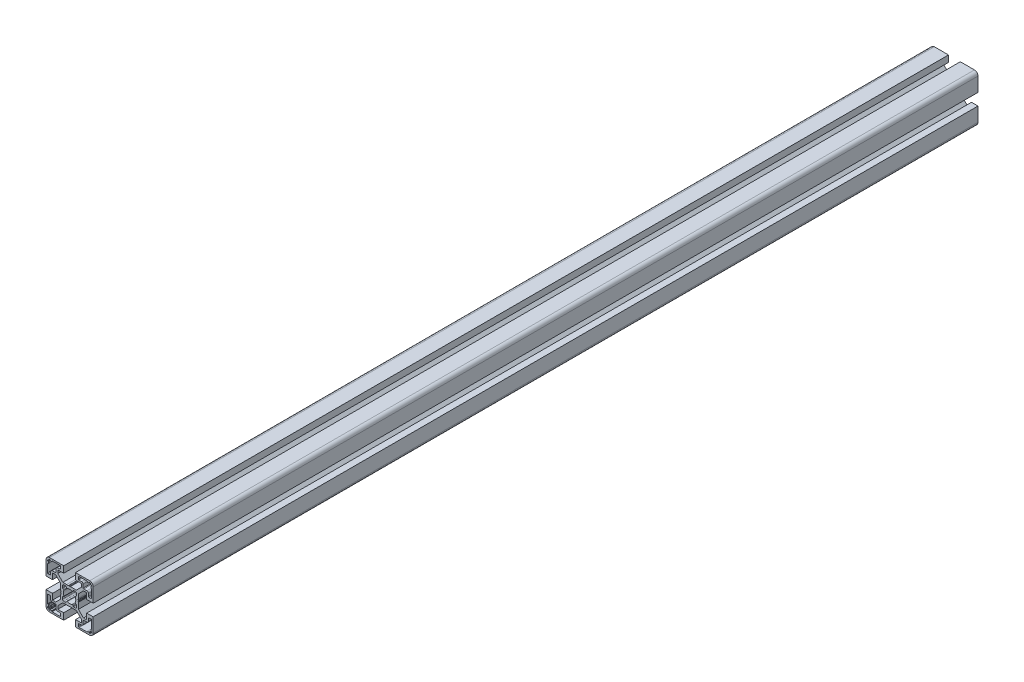
SolidWorks part; units mm, degrees
ref_plane "Front Plane" through (0, 0, 0) normal (0, 0, 1) x (1, 0, 0)
ref_plane "Top Plane" through (0, 0, 0) normal (0, 1, 0) x (1, 0, 0)
ref_plane "Right Plane" through (0, 0, 0) normal (1, 0, 0) x (0, 0, -1)
sketch "Sketch1" plane through (0, 0, 0) normal (0, 0, 1) x (1, 0, 0)
  line L0 (-11.7678, -10) -> (-14.5, -10)
  line L1 (-14.5, -10) -> (-14.5, -5)
  line L2 (-14.5, -5) -> (-20, -5)
  line L3 (-20, -5) -> (-20, -17)
  line L4 (-17, -20) -> (-5, -20)
  line L5 (-5, -20) -> (-5, -14.5)
  line L6 (-5, -14.5) -> (-10, -14.5)
  line L7 (-10, -14.5) -> (-10, -11.7678)
  line L8 (-10, -11.7678) -> (-5.7322, -7.5)
  line L9 (-5.7322, -7.5) -> (-0.6536, -7.5)
  line L10 (-0.4036, -7.433) -> (0, -7.2)
  line L11 (0, -7.2) -> (0.4036, -7.433)
  line L12 (0.9036, -7.433) -> (1.2189, -7.251)
  line L13 (1.2189, -7.251) -> (2.5, -7.5)
  line L14 (2.5, -7.5) -> (5.7322, -7.5)
  line L15 (5.7322, -7.5) -> (10, -11.7678)
  line L16 (10, -11.7678) -> (10, -14.5)
  line L17 (10, -14.5) -> (5, -14.5)
  line L18 (5, -14.5) -> (5, -20)
  line L19 (5, -20) -> (17, -20)
  line L20 (20, -17) -> (20, -5)
  line L21 (20, -5) -> (14.5, -5)
  line L22 (14.5, -5) -> (14.5, -10)
  line L23 (14.5, -10) -> (11.7678, -10)
  line L24 (11.7678, -10) -> (7.5, -5.7322)
  line L25 (7.5, -5.7322) -> (7.5, -0.6536)
  line L26 (7.433, -0.4036) -> (7.2, 0)
  line L27 (7.2, 0) -> (7.433, 0.4036)
  line L28 (7.433, 0.9036) -> (7.251, 1.2189)
  line L29 (7.251, 1.2189) -> (7.5, 2.5)
  line L30 (7.5, 2.5) -> (7.5, 5.7322)
  line L31 (7.5, 5.7322) -> (11.7678, 10)
  line L32 (11.7678, 10) -> (14.5, 10)
  line L33 (14.5, 10) -> (14.5, 5)
  line L34 (14.5, 5) -> (20, 5)
  line L35 (20, 5) -> (20, 17)
  line L36 (17, 20) -> (5, 20)
  line L37 (5, 20) -> (5, 14.5)
  line L38 (5, 14.5) -> (10, 14.5)
  line L39 (10, 14.5) -> (10, 11.7678)
  line L40 (10, 11.7678) -> (5.7322, 7.5)
  line L41 (5.7322, 7.5) -> (0.6536, 7.5)
  line L42 (0.4036, 7.433) -> (0, 7.2)
  line L43 (0, 7.2) -> (-0.4036, 7.433)
  line L44 (-0.9036, 7.433) -> (-1.2189, 7.251)
  line L45 (-1.2189, 7.251) -> (-2.5, 7.5)
  line L46 (-2.5, 7.5) -> (-5.7322, 7.5)
  line L47 (-5.7322, 7.5) -> (-10, 11.7678)
  line L48 (-10, 11.7678) -> (-10, 14.5)
  line L49 (-10, 14.5) -> (-5, 14.5)
  line L50 (-5, 14.5) -> (-5, 20)
  line L51 (-5, 20) -> (-17, 20)
  line L52 (-20, 17) -> (-20, 5)
  line L53 (-20, 5) -> (-14.5, 5)
  line L54 (-14.5, 5) -> (-14.5, 10)
  line L55 (-14.5, 10) -> (-11.7678, 10)
  line L56 (-11.7678, 10) -> (-7.5, 5.7322)
  line L57 (-7.5, 5.7322) -> (-7.5, 0.6536)
  line L58 (-7.433, 0.4036) -> (-7.2, 0)
  line L59 (-7.2, 0) -> (-7.433, -0.4036)
  line L60 (-7.433, -0.9036) -> (-7.251, -1.2189)
  line L61 (-7.251, -1.2189) -> (-7.5, -2.5)
  line L62 (-7.5, -2.5) -> (-7.5, -5.7322)
  line L63 (-7.5, -5.7322) -> (-11.7678, -10)
  line L64 (7.5, 16.5) -> (7.5, 18.2)
  line L65 (8, 18.7) -> (14.8, 18.7)
  line L66 (15, 18.5) -> (15, 18.2)
  line L67 (15.2, 18) -> (16.4, 18)
  line L68 (16.6, 18.2) -> (16.6, 18.5)
  line L69 (16.8, 18.7) -> (17.3, 18.7)
  line L70 (17.6, 18.4) -> (17.6, 17.9)
  line L71 (17.9, 17.6) -> (18.4, 17.6)
  line L72 (18.7, 17.3) -> (18.7, 16.8)
  line L73 (18.5, 16.6) -> (18.2, 16.6)
  line L74 (18, 16.4) -> (18, 15.2)
  line L75 (18.2, 15) -> (18.5, 15)
  line L76 (18.7, 14.8) -> (18.7, 8)
  line L77 (18.2, 7.5) -> (16.5, 7.5)
  line L78 (16, 8) -> (16, 10.2)
  line L79 (14.7, 11.5) -> (12, 11.5)
  line L80 (11.5, 12) -> (11.5, 14.7)
  line L81 (10.2, 16) -> (8, 16)
  line L82 (14.8, -18.7) -> (8, -18.7)
  line L83 (7.5, -18.2) -> (7.5, -16.5)
  line L84 (8, -16) -> (10.2, -16)
  line L85 (11.5, -14.7) -> (11.5, -12)
  line L86 (12, -11.5) -> (14.7, -11.5)
  line L87 (16, -10.2) -> (16, -8)
  line L88 (16.5, -7.5) -> (18.2, -7.5)
  line L89 (18.7, -8) -> (18.7, -14.8)
  line L90 (18.5, -15) -> (18.2, -15)
  line L91 (18, -15.2) -> (18, -16.4)
  line L92 (18.2, -16.6) -> (18.5, -16.6)
  line L93 (18.7, -16.8) -> (18.7, -17.3)
  line L94 (18.4, -17.6) -> (17.9, -17.6)
  line L95 (17.6, -17.9) -> (17.6, -18.4)
  line L96 (17.3, -18.7) -> (16.8, -18.7)
  line L97 (16.6, -18.5) -> (16.6, -18.2)
  line L98 (16.4, -18) -> (15.2, -18)
  line L99 (15, -18.2) -> (15, -18.5)
  line L100 (-18.7, 16.8) -> (-18.7, 17.3)
  line L101 (-18.4, 17.6) -> (-17.9, 17.6)
  line L102 (-17.6, 17.9) -> (-17.6, 18.4)
  line L103 (-17.3, 18.7) -> (-16.8, 18.7)
  line L104 (-16.6, 18.5) -> (-16.6, 18.2)
  line L105 (-16.4, 18) -> (-15.2, 18)
  line L106 (-15, 18.2) -> (-15, 18.5)
  line L107 (-14.8, 18.7) -> (-8, 18.7)
  line L108 (-7.5, 18.2) -> (-7.5, 16.5)
  line L109 (-8, 16) -> (-10.2, 16)
  line L110 (-11.5, 14.7) -> (-11.5, 12)
  line L111 (-12, 11.5) -> (-14.7, 11.5)
  line L112 (-16, 10.2) -> (-16, 8)
  line L113 (-16.5, 7.5) -> (-18.2, 7.5)
  line L114 (-18.7, 8) -> (-18.7, 14.8)
  line L115 (-18.5, 15) -> (-18.2, 15)
  line L116 (-18, 15.2) -> (-18, 16.4)
  line L117 (-18.2, 16.6) -> (-18.5, 16.6)
  line L118 (-18.7, -14.8) -> (-18.7, -8)
  line L119 (-18.2, -7.5) -> (-16.5, -7.5)
  line L120 (-16, -8) -> (-16, -10.2)
  line L121 (-14.7, -11.5) -> (-12, -11.5)
  line L122 (-11.5, -12) -> (-11.5, -14.7)
  line L123 (-10.2, -16) -> (-8, -16)
  line L124 (-7.5, -16.5) -> (-7.5, -18.2)
  line L125 (-8, -18.7) -> (-14.8, -18.7)
  line L126 (-15, -18.5) -> (-15, -18.2)
  line L127 (-15.2, -18) -> (-16.4, -18)
  line L128 (-16.6, -18.2) -> (-16.6, -18.5)
  line L129 (-16.8, -18.7) -> (-17.3, -18.7)
  line L130 (-17.6, -18.4) -> (-17.6, -17.9)
  line L131 (-17.9, -17.6) -> (-18.4, -17.6)
  line L132 (-18.7, -17.3) -> (-18.7, -16.8)
  line L133 (-18.5, -16.6) -> (-18.2, -16.6)
  line L134 (-18, -16.4) -> (-18, -15.2)
  line L135 (-18.2, -15) -> (-18.5, -15)
  line L136 (-6, 3.4907) -> (-6, 5)
  line L137 (-5, 6) -> (-3.4907, 6)
  line L138 (-3.0492, 5.7347) -> (-2.6892, 5.0577)
  line L139 (2.6892, 5.0577) -> (3.0492, 5.7347)
  line L140 (3.4907, 6) -> (5, 6)
  line L141 (6, 5) -> (6, 3.4907)
  line L142 (5.7347, 3.0492) -> (5.0577, 2.6892)
  line L143 (5.0577, -2.6892) -> (5.7347, -3.0492)
  line L144 (6, -3.4907) -> (6, -5)
  line L145 (5, -6) -> (3.4907, -6)
  line L146 (3.0492, -5.7347) -> (2.6892, -5.0577)
  line L147 (-2.6892, -5.0577) -> (-3.0492, -5.7347)
  line L148 (-3.4907, -6) -> (-5, -6)
  line L149 (-6, -5) -> (-6, -3.4907)
  line L150 (-5.7347, -3.0492) -> (-5.0577, -2.6892)
  line L151 (-5.0577, 2.6892) -> (-5.7347, 3.0492)
  arc A0 (-20, -17) -> (-17, -20) centre (-17, -17) ccw
  arc A1 (-0.6536, -7.5) -> (-0.4036, -7.433) centre (-0.6536, -7) ccw
  arc A2 (0.4036, -7.433) -> (0.9036, -7.433) centre (0.6536, -7) ccw
  arc A3 (17, -20) -> (20, -17) centre (17, -17) ccw
  arc A4 (7.5, -0.6536) -> (7.433, -0.4036) centre (7, -0.6536) ccw
  arc A5 (7.433, 0.4036) -> (7.433, 0.9036) centre (7, 0.6536) ccw
  arc A6 (20, 17) -> (17, 20) centre (17, 17) ccw
  arc A7 (0.6536, 7.5) -> (0.4036, 7.433) centre (0.6536, 7) ccw
  arc A8 (-0.4036, 7.433) -> (-0.9036, 7.433) centre (-0.6536, 7) ccw
  arc A9 (-17, 20) -> (-20, 17) centre (-17, 17) ccw
  arc A10 (-7.5, 0.6536) -> (-7.433, 0.4036) centre (-7, 0.6536) ccw
  arc A11 (-7.433, -0.4036) -> (-7.433, -0.9036) centre (-7, -0.6536) ccw
  arc A12 (8, 16) -> (7.5, 16.5) centre (8, 16.5) cw
  arc A13 (7.5, 18.2) -> (8, 18.7) centre (8, 18.2) cw
  arc A14 (14.8, 18.7) -> (15, 18.5) centre (14.8, 18.5) cw
  arc A15 (15, 18.2) -> (15.2, 18) centre (15.2, 18.2) ccw
  arc A16 (16.4, 18) -> (16.6, 18.2) centre (16.4, 18.2) ccw
  arc A17 (16.6, 18.5) -> (16.8, 18.7) centre (16.8, 18.5) cw
  arc A18 (17.3, 18.7) -> (17.6, 18.4) centre (17.3, 18.4) cw
  arc A19 (17.6, 17.9) -> (17.9, 17.6) centre (17.9, 17.9) ccw
  arc A20 (18.4, 17.6) -> (18.7, 17.3) centre (18.4, 17.3) cw
  arc A21 (18.7, 16.8) -> (18.5, 16.6) centre (18.5, 16.8) cw
  arc A22 (18.2, 16.6) -> (18, 16.4) centre (18.2, 16.4) ccw
  arc A23 (18, 15.2) -> (18.2, 15) centre (18.2, 15.2) ccw
  arc A24 (18.5, 15) -> (18.7, 14.8) centre (18.5, 14.8) cw
  arc A25 (18.7, 8) -> (18.2, 7.5) centre (18.2, 8) cw
  arc A26 (16.5, 7.5) -> (16, 8) centre (16.5, 8) cw
  arc A27 (16, 10.2) -> (14.7, 11.5) centre (14.7, 10.2) ccw
  arc A28 (12, 11.5) -> (11.5, 12) centre (12, 12) cw
  arc A29 (11.5, 14.7) -> (10.2, 16) centre (10.2, 14.7) ccw
  arc A30 (8, -18.7) -> (7.5, -18.2) centre (8, -18.2) cw
  arc A31 (7.5, -16.5) -> (8, -16) centre (8, -16.5) cw
  arc A32 (10.2, -16) -> (11.5, -14.7) centre (10.2, -14.7) ccw
  arc A33 (11.5, -12) -> (12, -11.5) centre (12, -12) cw
  arc A34 (14.7, -11.5) -> (16, -10.2) centre (14.7, -10.2) ccw
  arc A35 (16, -8) -> (16.5, -7.5) centre (16.5, -8) cw
  arc A36 (18.2, -7.5) -> (18.7, -8) centre (18.2, -8) cw
  arc A37 (18.7, -14.8) -> (18.5, -15) centre (18.5, -14.8) cw
  arc A38 (18.2, -15) -> (18, -15.2) centre (18.2, -15.2) ccw
  arc A39 (18, -16.4) -> (18.2, -16.6) centre (18.2, -16.4) ccw
  arc A40 (18.5, -16.6) -> (18.7, -16.8) centre (18.5, -16.8) cw
  arc A41 (18.7, -17.3) -> (18.4, -17.6) centre (18.4, -17.3) cw
  arc A42 (17.9, -17.6) -> (17.6, -17.9) centre (17.9, -17.9) ccw
  arc A43 (17.6, -18.4) -> (17.3, -18.7) centre (17.3, -18.4) cw
  arc A44 (16.8, -18.7) -> (16.6, -18.5) centre (16.8, -18.5) cw
  arc A45 (16.6, -18.2) -> (16.4, -18) centre (16.4, -18.2) ccw
  arc A46 (15.2, -18) -> (15, -18.2) centre (15.2, -18.2) ccw
  arc A47 (15, -18.5) -> (14.8, -18.7) centre (14.8, -18.5) cw
  arc A48 (-18.5, 16.6) -> (-18.7, 16.8) centre (-18.5, 16.8) cw
  arc A49 (-18.7, 17.3) -> (-18.4, 17.6) centre (-18.4, 17.3) cw
  arc A50 (-17.9, 17.6) -> (-17.6, 17.9) centre (-17.9, 17.9) ccw
  arc A51 (-17.6, 18.4) -> (-17.3, 18.7) centre (-17.3, 18.4) cw
  arc A52 (-16.8, 18.7) -> (-16.6, 18.5) centre (-16.8, 18.5) cw
  arc A53 (-16.6, 18.2) -> (-16.4, 18) centre (-16.4, 18.2) ccw
  arc A54 (-15.2, 18) -> (-15, 18.2) centre (-15.2, 18.2) ccw
  arc A55 (-15, 18.5) -> (-14.8, 18.7) centre (-14.8, 18.5) cw
  arc A56 (-8, 18.7) -> (-7.5, 18.2) centre (-8, 18.2) cw
  arc A57 (-7.5, 16.5) -> (-8, 16) centre (-8, 16.5) cw
  arc A58 (-10.2, 16) -> (-11.5, 14.7) centre (-10.2, 14.7) ccw
  arc A59 (-11.5, 12) -> (-12, 11.5) centre (-12, 12) cw
  arc A60 (-14.7, 11.5) -> (-16, 10.2) centre (-14.7, 10.2) ccw
  arc A61 (-16, 8) -> (-16.5, 7.5) centre (-16.5, 8) cw
  arc A62 (-18.2, 7.5) -> (-18.7, 8) centre (-18.2, 8) cw
  arc A63 (-18.7, 14.8) -> (-18.5, 15) centre (-18.5, 14.8) cw
  arc A64 (-18.2, 15) -> (-18, 15.2) centre (-18.2, 15.2) ccw
  arc A65 (-18, 16.4) -> (-18.2, 16.6) centre (-18.2, 16.4) ccw
  arc A66 (-18.5, -15) -> (-18.7, -14.8) centre (-18.5, -14.8) cw
  arc A67 (-18.7, -8) -> (-18.2, -7.5) centre (-18.2, -8) cw
  arc A68 (-16.5, -7.5) -> (-16, -8) centre (-16.5, -8) cw
  arc A69 (-16, -10.2) -> (-14.7, -11.5) centre (-14.7, -10.2) ccw
  arc A70 (-12, -11.5) -> (-11.5, -12) centre (-12, -12) cw
  arc A71 (-11.5, -14.7) -> (-10.2, -16) centre (-10.2, -14.7) ccw
  arc A72 (-8, -16) -> (-7.5, -16.5) centre (-8, -16.5) cw
  arc A73 (-7.5, -18.2) -> (-8, -18.7) centre (-8, -18.2) cw
  arc A74 (-14.8, -18.7) -> (-15, -18.5) centre (-14.8, -18.5) cw
  arc A75 (-15, -18.2) -> (-15.2, -18) centre (-15.2, -18.2) ccw
  arc A76 (-16.4, -18) -> (-16.6, -18.2) centre (-16.4, -18.2) ccw
  arc A77 (-16.6, -18.5) -> (-16.8, -18.7) centre (-16.8, -18.5) cw
  arc A78 (-17.3, -18.7) -> (-17.6, -18.4) centre (-17.3, -18.4) cw
  arc A79 (-17.6, -17.9) -> (-17.9, -17.6) centre (-17.9, -17.9) ccw
  arc A80 (-18.4, -17.6) -> (-18.7, -17.3) centre (-18.4, -17.3) cw
  arc A81 (-18.7, -16.8) -> (-18.5, -16.6) centre (-18.5, -16.8) cw
  arc A82 (-18.2, -16.6) -> (-18, -16.4) centre (-18.2, -16.4) ccw
  arc A83 (-18, -15.2) -> (-18.2, -15) centre (-18.2, -15.2) ccw
  arc A84 (-5.7347, 3.0492) -> (-6, 3.4907) centre (-5.5, 3.4907) cw
  arc A85 (-6, 5) -> (-5, 6) centre (-5, 5) cw
  arc A86 (-3.4907, 6) -> (-3.0492, 5.7347) centre (-3.4907, 5.5) cw
  arc A87 (-2.6892, 5.0577) -> (-2.0523, 4.8322) centre (-2.2478, 5.2925) ccw
  arc A88 (-2.0523, 4.8322) -> (2.0523, 4.8322) centre (0, 0) cw
  arc A89 (2.0523, 4.8322) -> (2.6892, 5.0577) centre (2.2478, 5.2925) ccw
  arc A90 (3.0492, 5.7347) -> (3.4907, 6) centre (3.4907, 5.5) cw
  arc A91 (5, 6) -> (6, 5) centre (5, 5) cw
  arc A92 (6, 3.4907) -> (5.7347, 3.0492) centre (5.5, 3.4907) cw
  arc A93 (5.0577, 2.6892) -> (4.8322, 2.0523) centre (5.2925, 2.2478) ccw
  arc A94 (4.8322, 2.0523) -> (4.8322, -2.0523) centre (0, 0) cw
  arc A95 (4.8322, -2.0523) -> (5.0577, -2.6892) centre (5.2925, -2.2478) ccw
  arc A96 (5.7347, -3.0492) -> (6, -3.4907) centre (5.5, -3.4907) cw
  arc A97 (6, -5) -> (5, -6) centre (5, -5) cw
  arc A98 (3.4907, -6) -> (3.0492, -5.7347) centre (3.4907, -5.5) cw
  arc A99 (2.6892, -5.0577) -> (2.0523, -4.8322) centre (2.2478, -5.2925) ccw
  arc A100 (2.0523, -4.8322) -> (-2.0523, -4.8322) centre (0, 0) cw
  arc A101 (-2.0523, -4.8322) -> (-2.6892, -5.0577) centre (-2.2478, -5.2925) ccw
  arc A102 (-3.0492, -5.7347) -> (-3.4907, -6) centre (-3.4907, -5.5) cw
  arc A103 (-5, -6) -> (-6, -5) centre (-5, -5) cw
  arc A104 (-6, -3.4907) -> (-5.7347, -3.0492) centre (-5.5, -3.4907) cw
  arc A105 (-5.0577, -2.6892) -> (-4.8322, -2.0523) centre (-5.2925, -2.2478) ccw
  arc A106 (-4.8322, -2.0523) -> (-4.8322, 2.0523) centre (0, 0) cw
  arc A107 (-4.8322, 2.0523) -> (-5.0577, 2.6892) centre (-5.2925, 2.2478) ccw
extrude "Boss-Extrude1" add sketch "Sketch1" against normal blind 750
